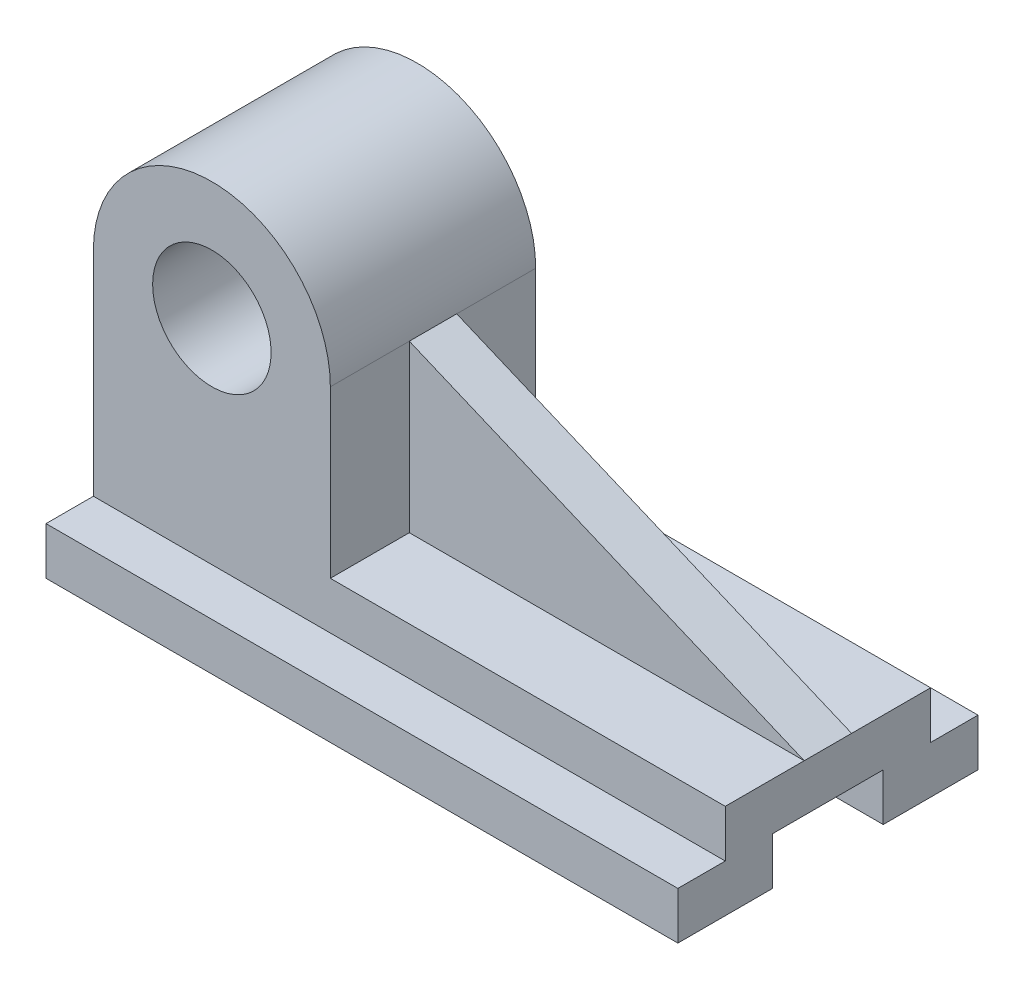
SolidWorks part; units mm, degrees
ref_plane "Front Plane" through (0, 0, 0) normal (0, 0, 1) x (1, 0, 0)
ref_plane "Top Plane" through (0, 0, 0) normal (0, 1, 0) x (1, 0, 0)
ref_plane "Right Plane" through (0, 0, 0) normal (1, 0, 0) x (0, 0, -1)
sketch "Sketch3" plane through (0, 0, 0) normal (0, 0, 1) x (1, 0, 0)
  line L1 (-80, 6) -> (80, 6)
  line L2 (-80, 6) -> (-80, -6)
  line L3 (-80, -6) -> (80, -6)
  line L4 (80, 6) -> (80, -6)
  line L5 (-80, 6) -> (80, -6) construction
  line L6 (-80, -6) -> (80, 6) construction
  point P0 (0, 0)
  dimension "D1" = 160
  dimension "D2" = 12
extrude "Boss-Extrude2" add sketch "Sketch3" against normal mid plane 52
sketch "Sketch4" plane through (0, 0, 26) normal (0, 0, 1) x (1, 0, 0)
  line L1 (-80, -6) -> (80, -6)
  line L2 (-80, -6) -> (-80, -18)
  line L3 (-80, -18) -> (80, -18)
  line L4 (80, -6) -> (80, -18)
  dimension "D1" = 160
  dimension "D2" = 12
extrude "Boss-Extrude3" add sketch "Sketch4" along normal mid plane 24
sketch "Sketch5" plane through (0, 0, -26) normal (0, 0, -1) x (-1, 0, 0)
  line L1 (-80, -6) -> (80, -6)
  line L2 (-80, -6) -> (-80, -18)
  line L3 (-80, -18) -> (80, -18)
  line L4 (80, -6) -> (80, -18)
  dimension "D1" = 160
  dimension "D2" = 12
extrude "Boss-Extrude4" add sketch "Sketch5" along normal mid plane 24
sketch "Sketch8" plane through (0, 0, -26) normal (0, 0, -1) x (-1, 0, 0)
  line L1 (80, 6) -> (20, 6)
  line L2 (80, 6) -> (80, 48)
  line L3 (80, 48) -> (20, 48)
  line L4 (20, 6) -> (20, 48)
  circle A0 centre (50, 48) radius 15
  arc A1 (80, 48) -> (20, 48) centre (50, 48) ccw
  line M6 (80, 6) -> (-80, 6)
  dimension "D3" = 30
  dimension "D1" = 42
  dimension "D2" = 60
extrude "Boss-Extrude5" add sketch "Sketch8" against normal blind 52 contours L3 A1 A0 | A0 L3 L4 L2 M6
sketch "Sketch14" plane through (0, 0, 0) normal (0, 0, 1) x (1, 0, 0)
  line L0 (-20, 48) -> (80, 6)
rib "Rib1" sketch "Sketch14" sketch "Sketch14" thickness 12 extrusion direction parallel to sketch draft on no parameters "D1"=12
